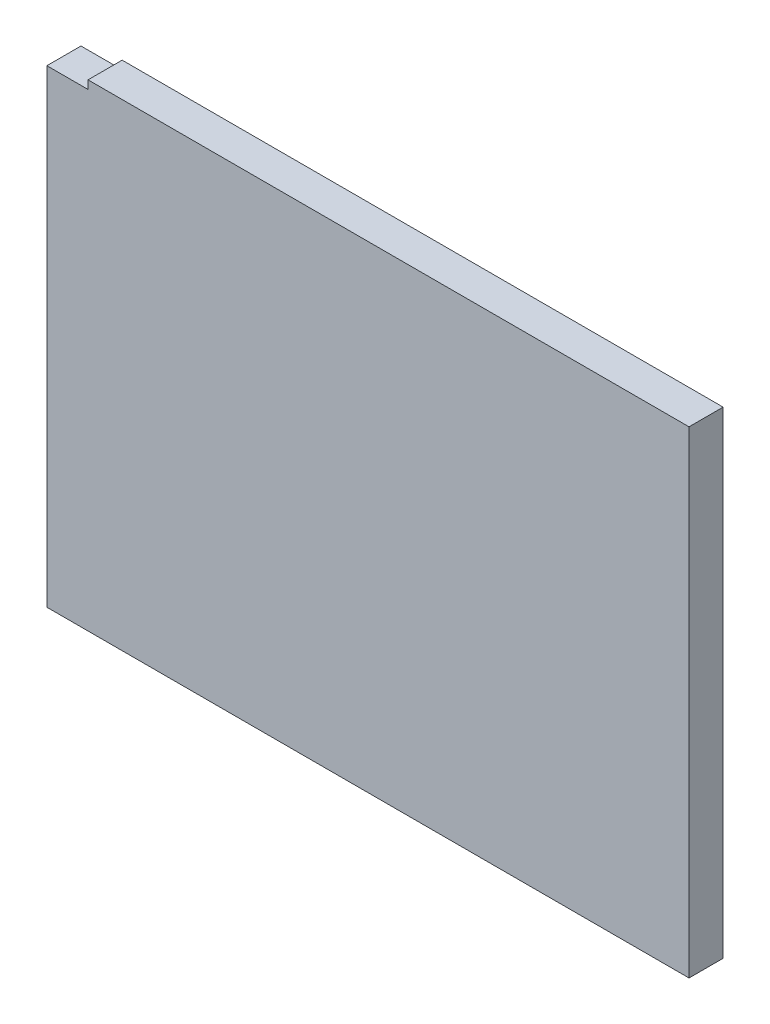
SolidWorks part; units mm, degrees
material "Pine"
ref_plane "Front Plane" through (0, 0, 0) normal (0, 0, 1) x (1, 0, 0)
ref_plane "Top Plane" through (0, 0, 0) normal (0, 1, 0) x (1, 0, 0)
ref_plane "Right Plane" through (0, 0, 0) normal (1, 0, 0) x (0, 0, -1)
sketch "Sketch1" plane through (0, 0, 0) normal (0, 0, 1) x (1, 0, 0)
  line L0 (-5300.6625, 1520.825) -> (-5451.475, 1520.825)
  line L1 (-5456.2375, 1384.3) -> (-5456.2375, 1516.0625)
  line L2 (-5557.8375, 1546.225) -> (-5194.3, 1546.225)
  line L3 (-5557.8375, 1539.875) -> (-5194.3, 1539.875)
  line L4 (-5297.4875, 1377.95) -> (-5454.65, 1377.95)
  line L5 (-5291.1375, 1384.3) -> (-5291.1375, 1516.0625)
  line L6 (-5300.6625, 1525.5875) -> (-5451.475, 1525.5875)
  line L7 (-5461, 1384.3) -> (-5461, 1516.0625)
  line L8 (-5297.4875, 1382.7125) -> (-5454.65, 1382.7125)
  line L9 (-5295.9, 1384.3) -> (-5295.9, 1516.0625)
  line L10 (-5740.4, 998.5375) -> (-5740.4, 1181.1)
  line L11 (-5740.4, 1181.1) -> (-5512.5938, 1181.1)
  line L12 (-5512.5938, 1181.1) -> (-5512.5938, 998.5375)
  line L13 (-5512.5938, 998.5375) -> (-5740.4, 998.5375)
  line L14 (-5258.5938, 1181.1) -> (-5486.4, 1181.1)
  line L15 (-5258.5938, 998.5375) -> (-5258.5938, 1181.1)
  line L16 (-5486.4, 998.5375) -> (-5258.5938, 998.5375)
  line L17 (-5486.4, 1181.1) -> (-5486.4, 998.5375)
  line L18 (-5740.4, 898.525) -> (-5011.7375, 898.525)
  line L19 (-5168.1062, 1384.3) -> (-5168.1062, 1392.2375)
  line L20 (-5176.0437, 1400.175) -> (-5245.8937, 1400.175)
  line L21 (-5253.8313, 1392.2375) -> (-5253.8313, 1384.3)
  line L22 (-5451.475, 1512.8875) -> (-5451.475, 1384.3)
  line L23 (-5303.8375, 1516.0625) -> (-5448.3, 1516.0625)
  line L24 (-5498.3062, 1384.3) -> (-5451.475, 1384.3)
  line L25 (-5253.8313, 1384.3) -> (-5300.6625, 1384.3)
  line L26 (-5584.0312, 1384.3) -> (-5740.4, 1384.3)
  line L27 (-5564.1875, 1536.7) -> (-5740.4, 1536.7)
  line L28 (-5740.4, 1357.3125) -> (-5740.4, 1206.5)
  line L29 (-5011.7375, 1357.3125) -> (-5740.4, 1357.3125)
  line L30 (-5011.7375, 1206.5) -> (-5011.7375, 1357.3125)
  line L31 (-5740.4, 1206.5) -> (-5011.7375, 1206.5)
  line L32 (-4765.675, 1549.4) -> (-4978.4, 1549.4)
  line L33 (-4765.675, 1397) -> (-4765.675, 1549.4)
  line L34 (-4978.4, 1397) -> (-4765.675, 1397)
  line L35 (-4978.4, 1549.4) -> (-4978.4, 1397)
  line L36 (-4765.675, 1371.6) -> (-4978.4, 1371.6)
  line L37 (-4765.675, 1219.2) -> (-4765.675, 1371.6)
  line L38 (-4978.4, 1219.2) -> (-4765.675, 1219.2)
  line L39 (-4978.4, 1371.6) -> (-4978.4, 1219.2)
  line L40 (-5284.7875, 803.275) -> (-5272.0875, 803.275)
  line L41 (-5187.95, 1536.7) -> (-5011.7375, 1536.7)
  line L42 (-5300.6625, 1384.3) -> (-5300.6625, 1512.8875)
  line L43 (-5740.4, 1536.7) -> (-5740.4, 1384.3)
  line L44 (-5557.8375, 1536.7) -> (-5557.8375, 1549.4)
  line L45 (-5557.8375, 1549.4) -> (-5194.3, 1549.4)
  line L46 (-5194.3, 1549.4) -> (-5194.3, 1536.7)
  line L47 (-5011.7375, 1536.7) -> (-5011.7375, 1384.3)
  line L48 (-5011.7375, 1384.3) -> (-5168.1062, 1384.3)
  line L49 (-5498.3062, 1384.3) -> (-5498.3062, 1392.2375)
  line L50 (-5506.2437, 1400.175) -> (-5576.0938, 1400.175)
  line L51 (-5584.0312, 1392.2375) -> (-5584.0312, 1384.3)
  line L52 (-5740.4, 660.4) -> (-5740.4, 898.525)
  line L53 (-5011.7375, 898.525) -> (-5011.7375, 660.4)
  line L54 (-5011.7375, 660.4) -> (-5740.4, 660.4)
  line L55 (-5291.1375, 803.275) -> (-5291.1375, 752.475)
  line L56 (-5265.7375, 752.475) -> (-5265.7375, 803.275)
  line L57 (-5284.7875, 752.475) -> (-5272.0875, 752.475)
  arc A0 (-5451.475, 1520.825) -> (-5456.2375, 1516.0625) centre (-5451.475, 1516.0625) ccw
  arc A1 (-5461, 1384.3) -> (-5454.65, 1377.95) centre (-5454.65, 1384.3) ccw
  arc A2 (-5297.4875, 1377.95) -> (-5291.1375, 1384.3) centre (-5297.4875, 1384.3) ccw
  circle A3 centre (-5037.9312, 1233.4875) radius 1.5875
  circle A4 centre (-5037.9312, 1328.7375) radius 1.5875
  circle A5 centre (-5714.2063, 1233.4875) radius 1.5875
  circle A6 centre (-5714.2063, 1328.7375) radius 1.5875
  circle A7 centre (-5018.0875, 1333.5) radius 1.5875
  circle A8 centre (-5018.0875, 1231.9) radius 1.5875
  circle A9 centre (-5734.05, 1231.9) radius 1.5875
  circle A10 centre (-5734.05, 1333.5) radius 1.5875
  circle A11 centre (-5734.05, 1511.3) radius 1.5875
  circle A12 centre (-5734.05, 1409.7) radius 1.5875
  circle A13 centre (-5018.0875, 1511.3) radius 1.5875
  circle A14 centre (-5018.0875, 1409.7) radius 1.5875
  arc A15 (-5557.8375, 1546.225) -> (-5557.8375, 1539.875) centre (-5557.8375, 1543.05) ccw
  arc A16 (-5194.3, 1539.875) -> (-5194.3, 1546.225) centre (-5194.3, 1543.05) ccw
  arc A17 (-5291.1375, 1516.0625) -> (-5300.6625, 1525.5875) centre (-5300.6625, 1516.0625) ccw
  arc A18 (-5451.475, 1525.5875) -> (-5461, 1516.0625) centre (-5451.475, 1516.0625) ccw
  arc A19 (-5456.2375, 1384.3) -> (-5454.65, 1382.7125) centre (-5454.65, 1384.3) ccw
  arc A20 (-5297.4875, 1382.7125) -> (-5295.9, 1384.3) centre (-5297.4875, 1384.3) ccw
  arc A21 (-5295.9, 1516.0625) -> (-5300.6625, 1520.825) centre (-5300.6625, 1516.0625) ccw
  circle A22 centre (-5702.3, 892.175) radius 1.5875
  circle A23 centre (-5734.05, 860.425) radius 1.5875
  circle A24 centre (-5474.8906, 892.175) radius 1.5875
  circle A25 centre (-5277.2469, 892.175) radius 1.5875
  circle A26 centre (-5049.8375, 892.175) radius 1.5875
  circle A27 centre (-5018.0875, 860.425) radius 1.5875
  circle A28 centre (-5296.6938, 1174.75) radius 1.5875
  circle A29 centre (-5448.3, 1174.75) radius 1.5875
  circle A30 centre (-5264.9437, 1155.7) radius 1.5875
  circle A31 centre (-5264.9437, 1023.9375) radius 1.5875
  circle A32 centre (-5518.9438, 1155.7) radius 1.5875
  circle A33 centre (-5518.9438, 1023.9375) radius 1.5875
  circle A34 centre (-5702.3, 1004.8875) radius 1.5875
  circle A35 centre (-5550.6937, 1004.8875) radius 1.5875
  arc A36 (-5576.0938, 1400.175) -> (-5584.0312, 1392.2375) centre (-5576.0938, 1392.2375) ccw
  arc A37 (-5168.1062, 1392.2375) -> (-5176.0437, 1400.175) centre (-5176.0437, 1392.2375) ccw
  arc A38 (-5245.8937, 1400.175) -> (-5253.8313, 1392.2375) centre (-5245.8937, 1392.2375) ccw
  arc A39 (-5448.3, 1516.0625) -> (-5451.475, 1512.8875) centre (-5448.3, 1512.8875) ccw
  arc A40 (-5284.7875, 803.275) -> (-5291.1375, 803.275) centre (-5287.9625, 803.275) ccw
  circle A41 centre (-5679.2812, 1026.3187) radius 1.5875
  circle A42 centre (-5679.2812, 1153.3187) radius 1.5875
  circle A43 centre (-5571.3313, 1153.3187) radius 1.5875
  circle A44 centre (-5571.3313, 1026.3187) radius 1.5875
  circle A45 centre (-5317.3312, 1153.3187) radius 1.5875
  circle A46 centre (-5317.3312, 1026.3187) radius 1.5875
  circle A47 centre (-5425.2812, 1026.3187) radius 1.5875
  circle A48 centre (-5425.2812, 1153.3187) radius 1.5875
  arc A49 (-5194.3, 1536.7) -> (-5187.95, 1536.7) centre (-5191.125, 1536.7) ccw
  arc A50 (-5564.1875, 1536.7) -> (-5557.8375, 1536.7) centre (-5561.0125, 1536.7) ccw
  arc A51 (-5300.6625, 1512.8875) -> (-5303.8375, 1516.0625) centre (-5303.8375, 1512.8875) ccw
  arc A52 (-5498.3062, 1392.2375) -> (-5506.2437, 1400.175) centre (-5506.2437, 1392.2375) ccw
  circle A53 centre (-5712.46, 784.225) radius 4.7625
  arc A54 (-5272.0875, 752.475) -> (-5265.7375, 752.475) centre (-5268.9125, 752.475) ccw
  arc A55 (-5291.1375, 752.475) -> (-5284.7875, 752.475) centre (-5287.9625, 752.475) ccw
  circle A56 centre (-5182.3938, 684.2125) radius 3.175
  circle A57 centre (-5239.5437, 684.2125) radius 3.175
  circle A58 centre (-5512.5938, 684.2125) radius 3.175
  circle A59 centre (-5569.7437, 684.2125) radius 3.175
  circle A60 centre (-5474.8906, 666.75) radius 1.5875
  circle A61 centre (-5277.2469, 666.75) radius 1.5875
  circle A62 centre (-5734.05, 698.5) radius 1.5875
  circle A63 centre (-5702.3, 666.75) radius 1.5875
  circle A64 centre (-5049.8375, 666.75) radius 1.5875
  circle A65 centre (-5018.0875, 698.5) radius 1.5875
  circle A66 centre (-5713.73, 835.025) radius 4.7625
  circle A67 centre (-5712.46, 819.785) radius 4.7625
  circle A68 centre (-5712.46, 802.005) radius 4.7625
  circle A69 centre (-5714.2063, 1314.45) radius 3.175
  circle A70 centre (-5037.9312, 1314.45) radius 3.175
  arc A71 (-5265.7375, 803.275) -> (-5272.0875, 803.275) centre (-5268.9125, 803.275) ccw
  ellipse E0 centre (-5371.3062, 1089.8188) end of major axis (-5277.6438, 1089.8188) minor radius 65.0875
  ellipse E1 centre (-5625.3062, 1089.8188) end of major axis (-5531.6438, 1089.8188) minor radius 65.0875
sketch "SideOutline" plane through (0, 0, 0) normal (0, 0, 1) x (1, 0, 0)
  line L0 (-4765.675, 1379.22) -> (-4765.675, 1219.2)
  line L1 (-4765.675, 1219.2) -> (-4980.94, 1219.2)
  line L2 (-4980.94, 1219.2) -> (-4980.94, 1379.22)
  line L3 (-4980.94, 1379.22) -> (-4765.675, 1379.22)
  line L8 (-4754.245, 1379.22) -> (-4982.0512, 1379.22) construction
extrude "SideOutline_Thickness" add sketch "SideOutline" against normal blind 11.43
sketch "Sketch2" plane through (0, 0, -11.43) normal (0, 0, -1) x (-1, 0, 0)
  line L0 (4980.94, 1376.426) -> (4967.1415, 1376.426)
  line L1 (4980.94, 1379.22) -> (4980.94, 1219.2) construction
  line L2 (4967.1415, 1376.426) -> (4998.485, 1376.426) construction
  line L3 (4967.1415, 1376.426) -> (4967.1415, 1379.22)
  line L4 (4765.675, 1379.22) -> (4980.94, 1379.22) construction
  line L5 (4967.1415, 1379.22) -> (4980.94, 1379.22)
  line L6 (4980.94, 1379.22) -> (4980.94, 1376.426)
extrude "Cut-Extrude1" cut sketch "Sketch2" against normal up to surface (11.43 mm away) up to face at (-4873.3075, 1299.21, 0)
